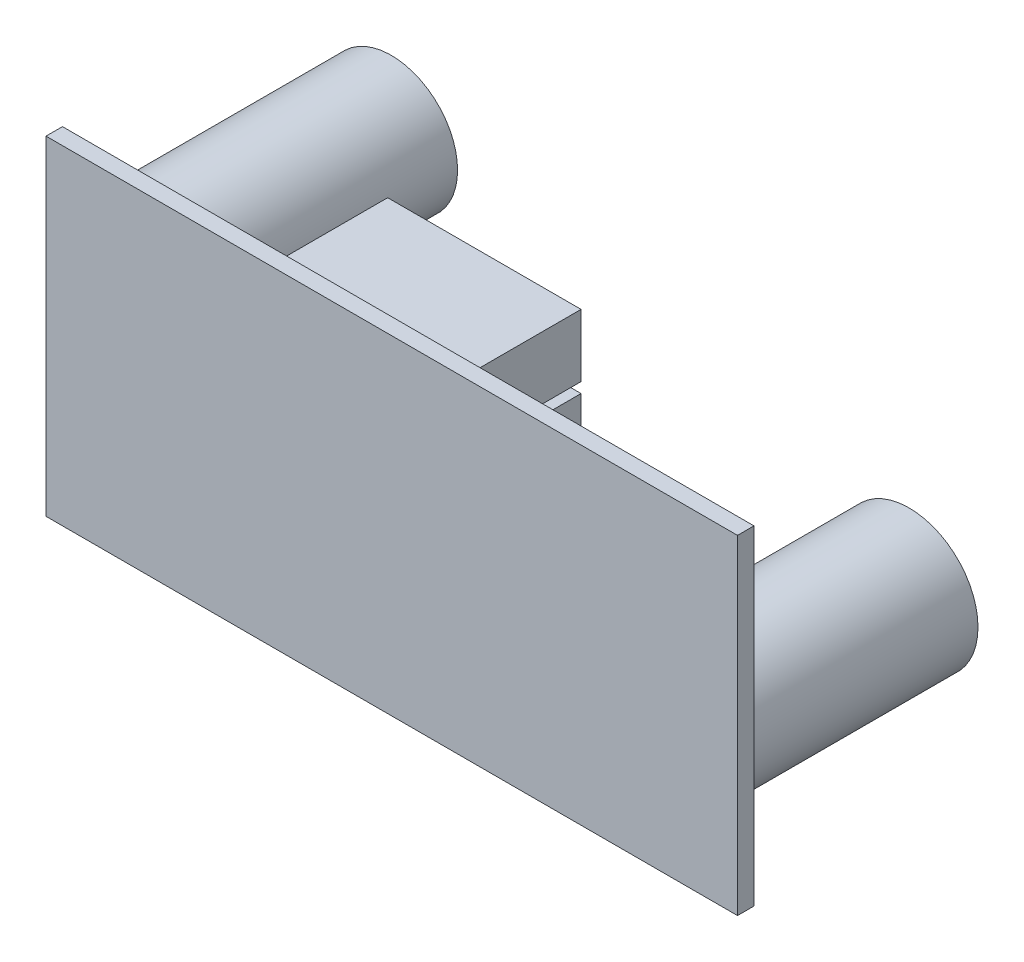
SolidWorks part; units mm, degrees
ref_plane "Front Plane" through (0, 0, 0) normal (0, 0, 1) x (1, 0, 0)
ref_plane "Top Plane" through (0, 0, 0) normal (0, 1, 0) x (1, 0, 0)
ref_plane "Right Plane" through (0, 0, 0) normal (1, 0, 0) x (0, 0, -1)
sketch "Sketch1" plane through (0, 0, 0) normal (0, 0, 1) x (1, 0, 0)
  line L1 (-25.9312, 5.2915) -> (16.0688, 5.2915)
  line L2 (-25.9312, 5.2915) -> (-25.9312, -14.7085)
  line L3 (-25.9312, -14.7085) -> (16.0688, -14.7085)
  line L4 (16.0688, 5.2915) -> (16.0688, -14.7085)
  dimension "D1" = 42
  dimension "D2" = 20
extrude "Boss-Extrude1" add sketch "Sketch1" along normal blind 1
sketch "Sketch2" plane through (0, 0, 0) normal (0, 0, 1) x (1, 0, 0)
  circle A0 centre (-20.9611, 0) radius 4.0279
  circle A1 centre (10.4931, -8.2347) radius 4.1827
extrude "Boss-Extrude2" add sketch "Sketch2" against normal blind 15
sketch "Sketch3" plane through (0, 0, 0) normal (0, 0, 1) x (1, 0, 0)
  line L1 (-13.1782, 4.4281) -> (-1.4331, 4.4281)
  line L2 (-13.1782, 4.4281) -> (-13.1782, 0.6274)
  line L3 (-13.1782, 0.6274) -> (-1.4331, 0.6274)
  line L4 (-1.4331, 4.4281) -> (-1.4331, 0.6274)
  line L5 (-13.1782, 0) -> (-1.4347, 0)
  line L6 (-13.1782, 0) -> (-13.1782, -12.9836)
  line L7 (-13.1782, -12.9836) -> (-1.4347, -12.9836)
  line L8 (-1.4347, 0) -> (-1.4347, -12.9836)
extrude "Boss-Extrude3" add sketch "Sketch3" against normal blind 7
